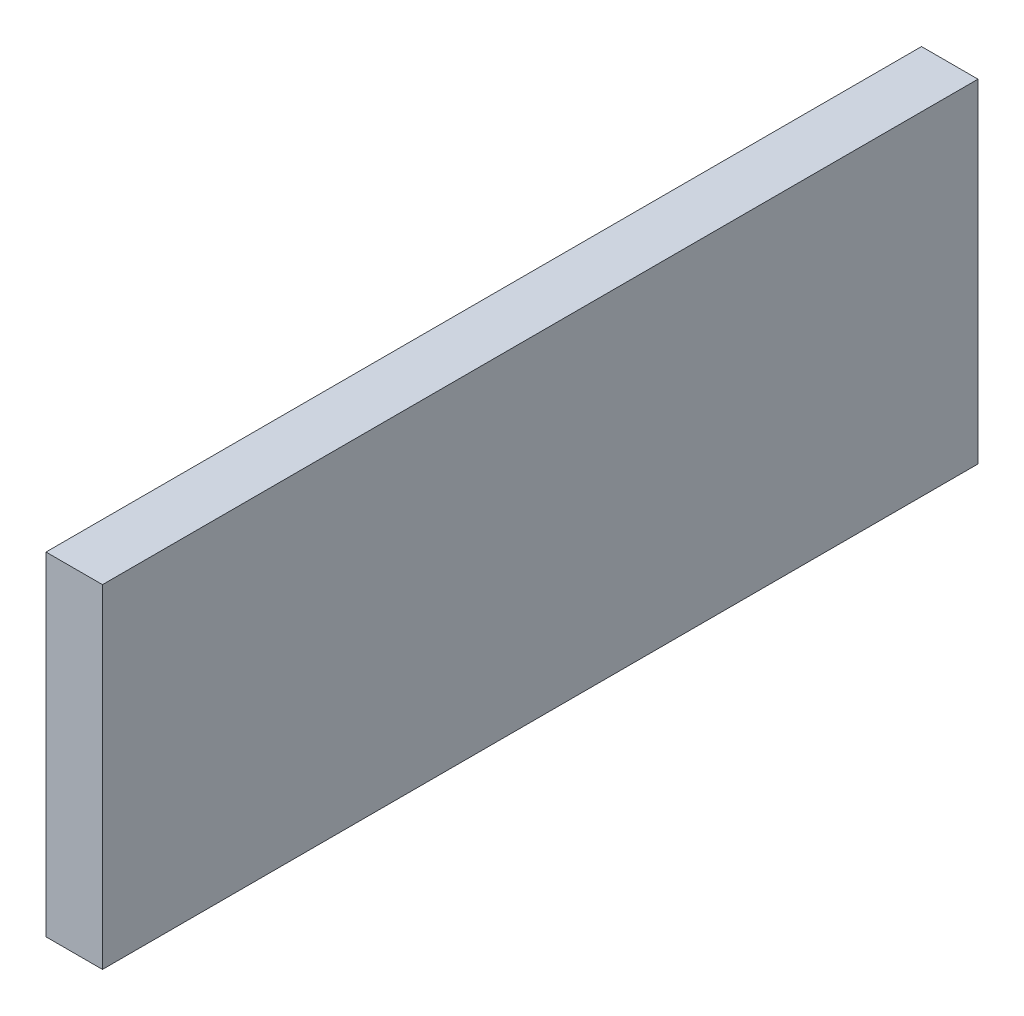
SolidWorks part; units mm, degrees
material "3.7VLiPoCell"
ref_plane "Front Plane" through (0, 0, 0) normal (0, 0, 1) x (1, 0, 0)
ref_plane "Top Plane" through (0, 0, 0) normal (0, 1, 0) x (1, 0, 0)
ref_plane "Right Plane" through (0, 0, 0) normal (1, 0, 0) x (0, 0, -1)
sketch "Sketch1" plane through (0, 0, 0) normal (0, 0, 1) x (1, 0, 0)
  line L1 (-5, 29.5) -> (5, 29.5)
  line L2 (-5, 29.5) -> (-5, -29.5)
  line L3 (-5, -29.5) -> (5, -29.5)
  line L4 (5, 29.5) -> (5, -29.5)
  dimension "D1" = 59
  dimension "D2" = 29.5
  dimension "D3" = 5
  dimension "D4" = 10
extrude "Extrude1" add sketch "Sketch1" along normal blind 155
